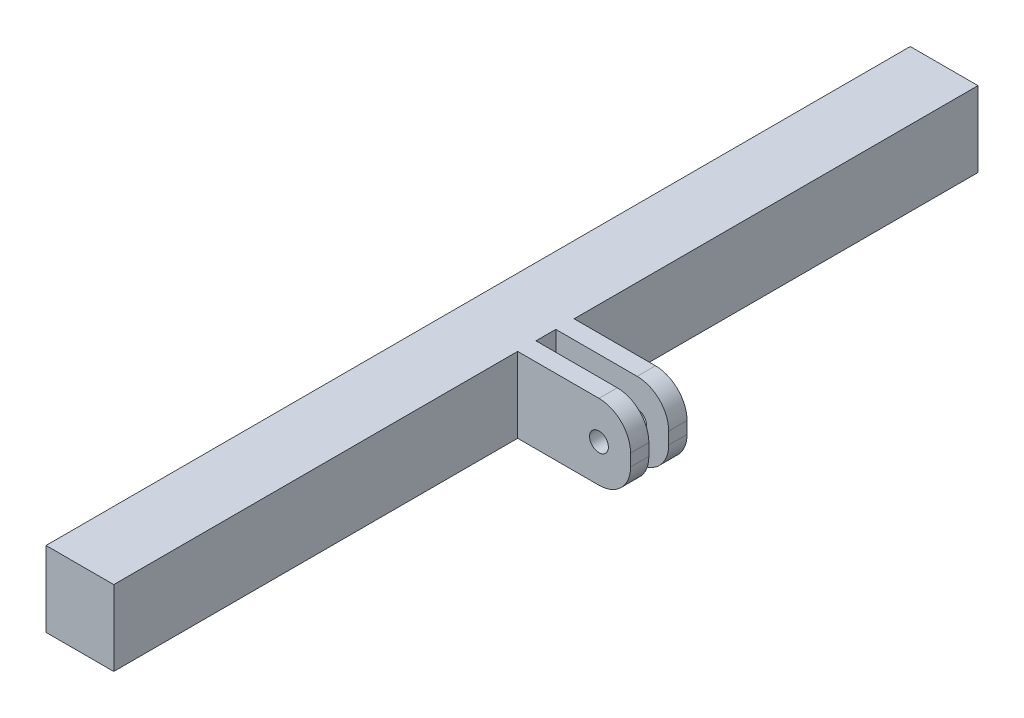
SolidWorks part; units mm, degrees
ref_plane "Front Plane" through (0, 0, 0) normal (0, 0, 1) x (1, 0, 0)
ref_plane "Top Plane" through (0, 0, 0) normal (0, 1, 0) x (1, 0, 0)
ref_plane "Right Plane" through (0, 0, 0) normal (1, 0, 0) x (0, 0, -1)
sketch "Sketch1" plane through (0, 0, 0) normal (0, 0, 1) x (1, 0, 0)
  line L5 (0, 0) -> (11.43, 0)
  line L6 (0, 0) -> (0, -12.7)
  line L7 (0, -12.7) -> (11.43, -12.7)
  line L8 (11.43, 0) -> (11.43, -12.7)
  dimension "D1" = 12.7
  dimension "D2" = 11.43
extrude "Boss-Extrude1" add sketch "Sketch1" along normal blind 72.898 and the other way blind 72.898
sketch "Sketch2" plane through (0, 0, 0) normal (0, 0, 1) x (1, 0, 0)
  line L0 (0, -12.7) -> (11.43, -12.7) construction
  line L1 (11.43, 0) -> (25.146, 0)
  line L2 (11.43, 0) -> (11.43, -12.7)
  line L3 (11.43, -12.7) -> (25.146, -12.7)
  line L4 (30.48, -5.334) -> (30.48, -7.366)
  line L5 (30.48, -6.35) -> (11.43, -6.35) construction
  line L6 (25.146, -5.334) -> (25.146, -7.366) construction
  arc A0 (30.48, -7.366) -> (25.146, -12.7) centre (25.146, -7.366) cw
  arc A1 (30.48, -5.334) -> (25.146, 0) centre (25.146, -5.334) ccw
  circle A2 centre (25.146, -6.35) radius 1.5875
  point P9 (30.48, -12.7)
  dimension "D2" = 5.334
  dimension "D3" = 3.175
  dimension "D1" = 19.05
extrude "Boss-Extrude2" add sketch "Sketch2" along normal blind 4.7625 and the other way blind 4.7625
sketch "Sketch3" plane through (0, 0, 0) normal (0, 0, 1) x (1, 0, 0)
  line L4 (11.43, 0) -> (11.43, -12.7)
  line L5 (11.43, -12.7) -> (25.146, -12.7)
  line L6 (30.48, -7.366) -> (30.48, -5.334)
  line L7 (25.146, 0) -> (11.43, 0)
  line L8 (11.43, 0) -> (11.43, -12.7)
  line L9 (11.43, -12.7) -> (25.146, -12.7)
  line L10 (30.48, -7.366) -> (30.48, -5.334)
  line L11 (25.146, 0) -> (11.43, 0)
  arc A2 (25.146, -12.7) -> (30.48, -7.366) centre (25.146, -7.366) ccw
  arc A3 (30.48, -5.334) -> (25.146, 0) centre (25.146, -5.334) ccw
  arc A4 (25.146, -12.7) -> (30.48, -7.366) centre (25.146, -7.366) ccw
  arc A5 (30.48, -5.334) -> (25.146, 0) centre (25.146, -5.334) ccw
  dimension "D1" = 0
extrude "Cut-Extrude1" cut sketch "Sketch3" against normal blind 1.6764 and the other way blind 1.6764
